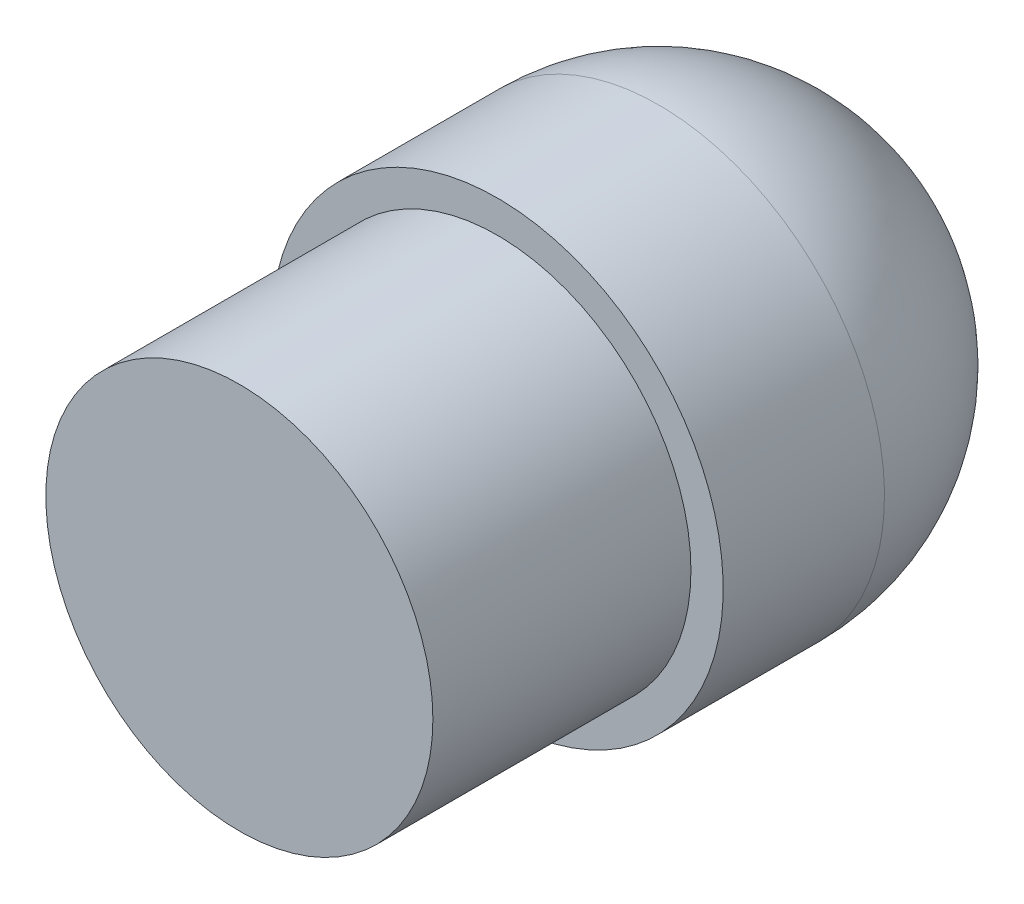
SolidWorks part; units mm, degrees
ref_plane "Ön Düzlem" through (0, 0, 0) normal (0, 0, 1) x (1, 0, 0)
ref_plane "Üst Düzlem" through (0, 0, 0) normal (0, 1, 0) x (1, 0, 0)
ref_plane "Sağ Düzlem" through (0, 0, 0) normal (1, 0, 0) x (0, 0, -1)
sketch "Çizim3" plane through (0, 0, 0) normal (0, 0, 1) x (1, 0, 0)
  circle A0 centre (0, 0) radius 15
  dimension "D1" = 30
extrude "Yükseklik-Ekstrüzyon1" add sketch "Çizim3" against normal blind 20
sketch "Çizim4" plane through (0, 0, -20) normal (0, 0, -1) x (-1, 0, 0)
  circle A0 centre (0, 0) radius 17.5
  dimension "D1" = 35
extrude "Yükseklik-Ekstrüzyon2" add sketch "Çizim4" along normal blind 12.5
sketch "Çizim5" plane through (0, 0, 0) normal (1, 0, 0) x (0, 0, -1)
  line L0 (32.5, 0) -> (48.0865, 0) construction
  line L1 (32.5, -17.5) -> (32.5, 17.5) construction
  line L2 (50, 0) -> (32.5, 0)
  line L3 (32.5, 0) -> (32.5, -17.5)
  arc A1 (32.5, -17.5) -> (50, 0) centre (32.5, 0) ccw
  dimension "D1" = 50
revolve "Döndür4" add sketch "Çizim5" angle 360 about L0
